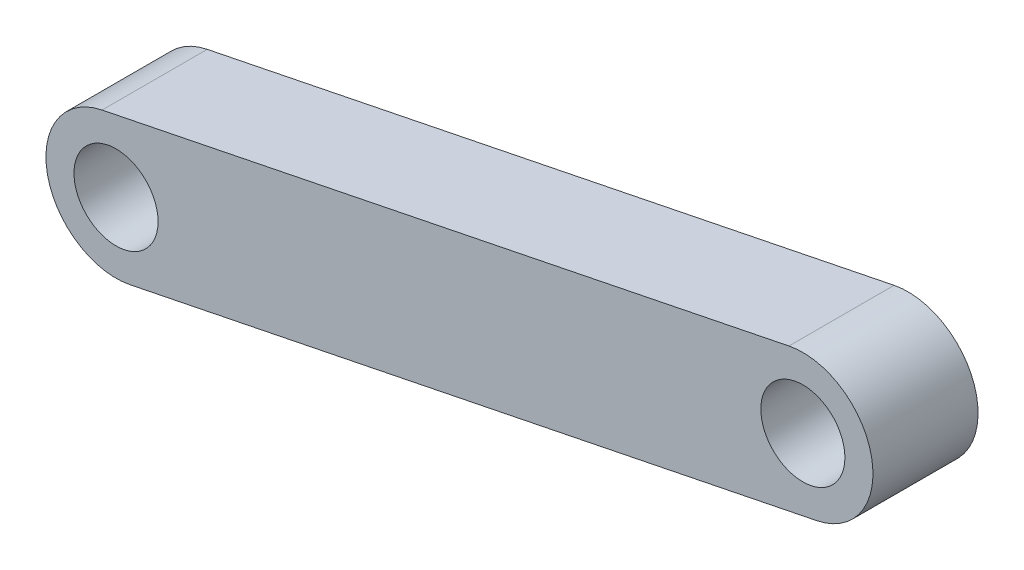
SolidWorks part; units mm, degrees
ref_plane "Front Plane" through (0, 0, 0) normal (0, 0, 1) x (1, 0, 0)
ref_plane "Top Plane" through (0, 0, 0) normal (0, 1, 0) x (1, 0, 0)
ref_plane "Right Plane" through (0, 0, 0) normal (1, 0, 0) x (0, 0, -1)
sketch "Sketch1" plane through (0, 0, 0) normal (0, 0, 1) x (1, 0, 0)
  line L0 (0, 0) -> (196.0221, 39.6903) construction
  line L1 (-3.969, 19.6022) -> (192.0531, 59.2925)
  line L2 (3.969, -19.6022) -> (199.9912, 20.0881)
  arc A0 (-3.969, 19.6022) -> (3.969, -19.6022) centre (0, 0) ccw
  arc A1 (199.9912, 20.0881) -> (192.0531, 59.2925) centre (196.0221, 39.6903) ccw
  circle A2 centre (0, 0) radius 12
  circle A3 centre (196.0221, 39.6903) radius 12
  point P3 (98.0111, 19.8452)
  point P12 (147.4486, 135.1255)
  point P13 (199.9557, 4.2101)
  dimension "D1" = 200
  dimension "D2" = 24
  dimension "D3" = 40
extrude "Boss-Extrude1" add sketch "Sketch1" along normal blind 30
